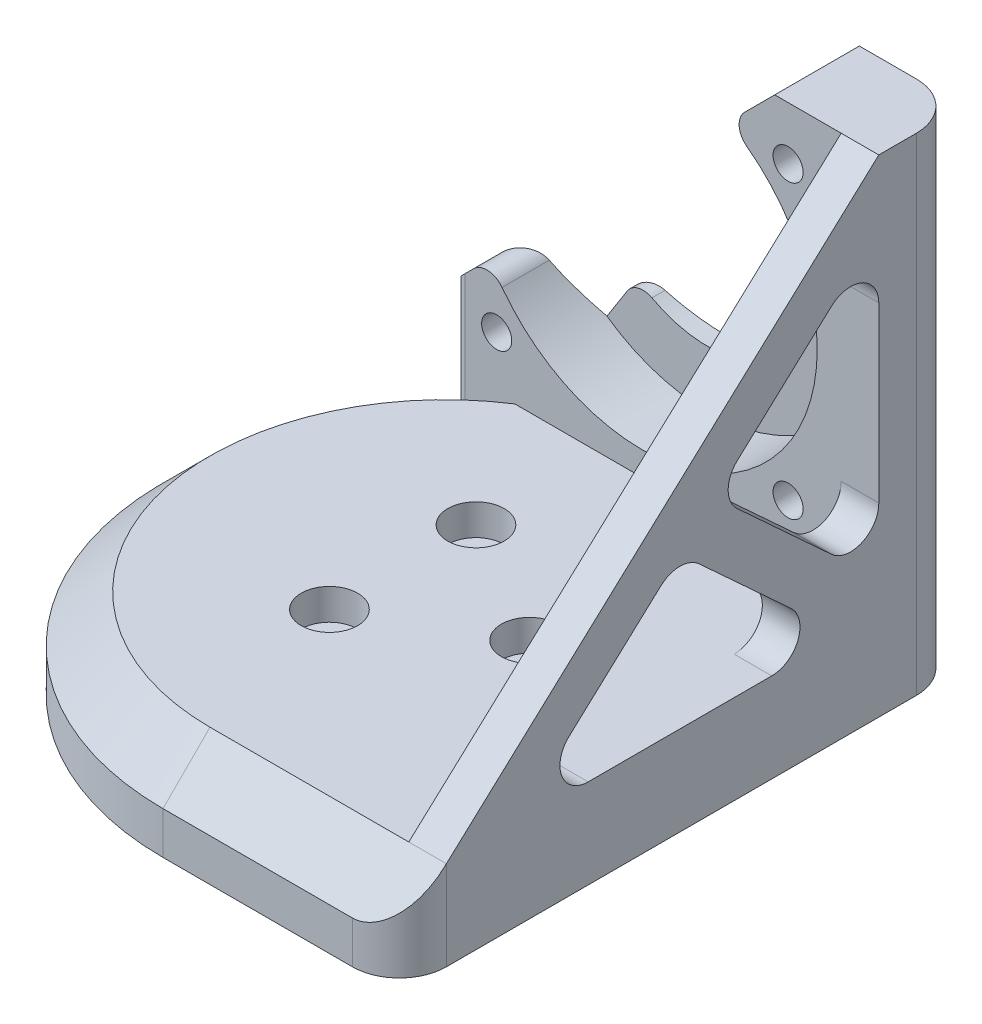
SolidWorks part; units mm, degrees
ref_plane "前视基准面" through (0, 0, 0) normal (0, 0, 1) x (1, 0, 0)
ref_plane "上视基准面" through (0, 0, 0) normal (0, 1, 0) x (1, 0, 0)
ref_plane "右视基准面" through (0, 0, 0) normal (1, 0, 0) x (0, 0, -1)
other "Configuration Table"
sketch "草图1" plane through (0, 0, 0) normal (0, 1, 0) x (1, 0, 0)
  line L0 (0, 0) -> (9, 0) construction
  line L1 (0, 0) -> (-4.5, -7.7942) construction
  circle A0 centre (0, 0) radius 12.4
  circle A1 centre (9, 0) radius 1.6
  circle A2 centre (-4.5, -7.7942) radius 1.6
  circle A3 centre (-4.5, 7.7942) radius 1.6
  dimension "D1" = 24.8
  dimension "D2" = 9
  dimension "D3" = 3.2
  dimension "D5" = 120
  dimension "D4" = 3
extrude "凸台-拉伸1" add sketch "草图1" along normal blind 20
sketch "草图2" plane through (0, 20, 0) normal (0, 1, 0) x (1, 0, 0)
  line L0 (0, 30) -> (25.15, 30)
  line L1 (25.15, 30) -> (25.15, -30)
  line L2 (25.15, -30) -> (0, -30)
  arc A0 (0, 30) -> (0, -30) centre (0, 0) ccw
  circle A1 centre (0, 0) radius 12.4
  circle A2 centre (0, 0) radius 12.4 construction
  dimension "D1" = 60
  dimension "D2" = 25.15
extrude "凸台-拉伸2" add sketch "草图2" against normal blind 9.5
sketch "草图4" plane through (0, 20, 0) normal (0, 1, 0) x (1, 0, 0)
  circle A0 centre (9, 0) radius 3
  circle A1 centre (-4.5, 7.7942) radius 3
  circle A2 centre (-4.5, -7.7942) radius 3
  dimension "D1" = 6
extrude "切除-拉伸1" cut sketch "草图4" against normal blind 3.3
sketch "草图5" plane through (0, 0, -30) normal (0, 0, -1) x (-1, 0, 0)
  line L0 (-25.15, 20) -> (-25.15, 62.3)
  line L2 (-25.15, 20) -> (0, 20) construction
  line L3 (28.2211, 20) -> (-25.15, 20)
  line L4 (-25.15, 62.3) -> (-14.0789, 62.3)
  line L5 (-14.0789, 62.3) -> (28.2211, 20)
  circle A0 centre (-15.5, 25.65) radius 1.6
  circle A1 centre (-15.5, 56.65) radius 1.6
  circle A2 centre (15.5, 25.65) radius 1.6
  dimension "D1" = 31
  dimension "D2" = 5.65
  dimension "D4" = 5
  dimension "D5" = 9.65
  dimension "D6" = 3.2
  dimension "D7" = 31
  dimension "D8" = 5
  dimension "D3" = 42.3
extrude "凸台-拉伸3" add sketch "草图5" against normal blind 9
sketch "草图6" plane through (25.15, 0, 0) normal (1, 0, 0) x (0, 0, -1)
  line L0 (-25, 20) -> (21, 62.3)
  line L1 (21, 62.3) -> (21, 20)
  line L2 (21, 20) -> (-25, 20)
  line L3 (-30, 10.5) -> (-30, 20) construction
  dimension "D1" = 5
extrude "凸台-拉伸4" add sketch "草图6" against normal blind 4
sketch "草图7" plane through (0, 20, 0) normal (0, -1, 0) x (1, 0, 0)
  line L2 (-28.2211, -30) -> (0, -30)
  line L3 (-28.2211, -21) -> (-28.2211, -30)
  line L4 (-28.2211, -30) -> (0, -30)
  line L5 (-28.2211, -21) -> (-28.2211, -30)
  line L7 (-21.4243, -21) -> (-28.2211, -21)
  line L8 (-21.4243, -21) -> (-28.2211, -21)
  arc A1 (-21.4243, -21) -> (0, -30) centre (0, 0) ccw
  arc A2 (-21.4243, -21) -> (0, -30) centre (0, 0) ccw
  dimension "D1" = 0
extrude "切除-拉伸2" cut sketch "草图7" against normal through all
sketch "草图8" plane through (0, 0, -30) normal (0, 0, -1) x (-1, 0, 0)
  circle A0 centre (-15.5, 56.65) radius 3
  circle A1 centre (-15.5, 25.65) radius 3
  dimension "D1" = 6
extrude "切除-拉伸3" cut sketch "草图8" against normal blind 3.3 and the other way through all
sketch "草图9" plane through (0, 0, -21) normal (0, 0, 1) x (1, 0, 0)
  line L0 (15.5, 56.65) -> (-15.5, 25.65) construction
  circle A0 centre (0, 41.15) radius 18.6
  dimension "D1" = 37.2
chamfer "倒角1" distance 5 angle 45 2 edges at (12.575, 20, 30) (-27.6586, 20, 11.619)
extrude "凸台-拉伸7" add sketch "草图9" against normal up to surface (9 mm away) up to face at (12.5, 56.65, -30)
sketch "草图17" plane through (0, 10.5, 0) normal (0, -1, 0) x (1, 0, 0)
  line L0 (0, -30) -> (-18.6, -30)
  line L1 (-18.6, -30) -> (-18.6, -23.5381)
  line L2 (-18.6, -21) -> (-18.6, -30) construction
  arc A0 (0, 30) -> (0, -30) centre (0, 0) ccw construction
  arc A1 (-18.6, -23.5381) -> (0, -30) centre (0, 0) ccw
extrude "切除-拉伸7" cut sketch "草图17" against normal through all
sketch "草图18" plane through (0, 0, -21) normal (0, 0, 1) x (1, 0, 0)
  circle A1 centre (-15.5, 25.65) radius 1.6 construction
  circle A2 centre (-15.5, 25.65) radius 1.6
  circle A3 centre (-15.5, 25.65) radius 3
  dimension "D1" = 6
extrude "凸台-拉伸8" add sketch "草图18" against normal up to surface (5.7 mm away) up to face at (12.5, 25.65, -26.7)
sketch "草图19" plane through (0, 0, -26.7) normal (0, 0, -1) x (-1, 0, 0)
  circle A0 centre (15.5, 25.65) radius 3
  dimension "D1" = 6
extrude "切除-拉伸8" cut sketch "草图19" along normal through all
sketch "草图20" plane through (0, 0, -21) normal (0, 0, 1) x (1, 0, 0)
  circle A0 centre (0, 41.15) radius 18.6
  arc A1 (9.1325, 57.3536) -> (-16.2036, 32.0175) centre (0, 41.15) ccw construction
  dimension "D1" = 37.2
extrude "切除-拉伸9" cut sketch "草图20" against normal blind 7
sketch "草图21" plane through (0, 0, -28) normal (0, 0, 1) x (1, 0, 0)
  line L0 (9.1325, 57.3536) -> (-10.7703, 25.9856)
  line L1 (-10.7703, 25.9856) -> (-10.7703, 56.3144)
  arc A0 (9.1325, 57.3536) -> (-10.7703, 56.3144) centre (0, 41.15) ccw construction
  arc A1 (9.1325, 57.3536) -> (-10.7703, 56.3144) centre (0, 41.15) ccw
extrude "切除-拉伸10" cut sketch "草图21" against normal blind 7
fillet "圆角2" radius 2 2 edges at (9.1325, 57.3536, -24.5) (-16.2036, 32.0175, -23.1238)
sketch "草图22" plane through (0, 0, -28) normal (0, 0, 1) x (1, 0, 0)
  circle A0 centre (0, 41.15) radius 12.6
  arc A1 (-14.9273, 30.0534) -> (11.0966, 56.0773) centre (0, 41.15) ccw construction
  dimension "D1" = 25.2
extrude "切除-拉伸11" cut sketch "草图22" against normal blind 7
fillet "圆角3" radius 2 2 edges at (5.9116, 52.2772, -29) (-7.5493, 31.062, -28.5173)
sketch "草图23" plane through (21.15, 0, 0) normal (-1, 0, 0) x (0, 0, 1)
  line L0 (-21, 55.5074) -> (-21, 20)
  line L1 (-21, 20) -> (17.6132, 20)
  line L2 (17.6132, 20) -> (-21, 55.5074)
  line L3 (-21, 23.3963) -> (-3.5401, 39.4518)
  line L4 (-17.3066, 20) -> (0.1533, 36.0555)
  line L5 (-1.6934, 37.7537) -> (-21, 20) construction
  line L6 (-21, 62.3) -> (25, 20) construction
  line L9 (25, 20) -> (-21, 20) construction
  line M9 (-21, 62.3) -> (-21, 20)
  dimension "D1" = 5
  dimension "D2" = 2.5
  dimension "D3" = 2.5
extrude "切除-拉伸12" cut sketch "草图23" against normal through all contours L3 L2 M9 | L4 L1 L2
fillet "圆角4" radius 3 6 edges at (23.15, 55.5074, -21) (23.15, 39.4518, -3.5401) (23.15, 23.3963, -21) (23.15, 20, -17.3066) (23.15, 36.0555, 0.1533) (23.15, 20, 17.6132)
sketch "草图24" plane through (0, 20, 0) normal (0, 1, 0) x (1, 0, 0)
  line L0 (0, -25) -> (21.15, -25) construction
  line L1 (25.15, -25) -> (25.15, -30) construction
  line L2 (25.15, -30) -> (0, -30) construction
  line L3 (25.15, -25) -> (25.15, -30)
  line L4 (25.15, -30) -> (20.15, -30)
  arc A0 (25.15, -25) -> (20.15, -30) centre (20.15, -25) cw
extrude "切除-拉伸13" cut sketch "草图24" against normal through all
fillet "圆角5" radius 1 1 edges at (-21.4243, 20.8984, -21)
fillet "圆角6" radius 5 1 edges at (25.15, 36.4, -30)
chamfer "倒角2" distance 1 angle 45 1 edges at (0, 0, 12.4)
